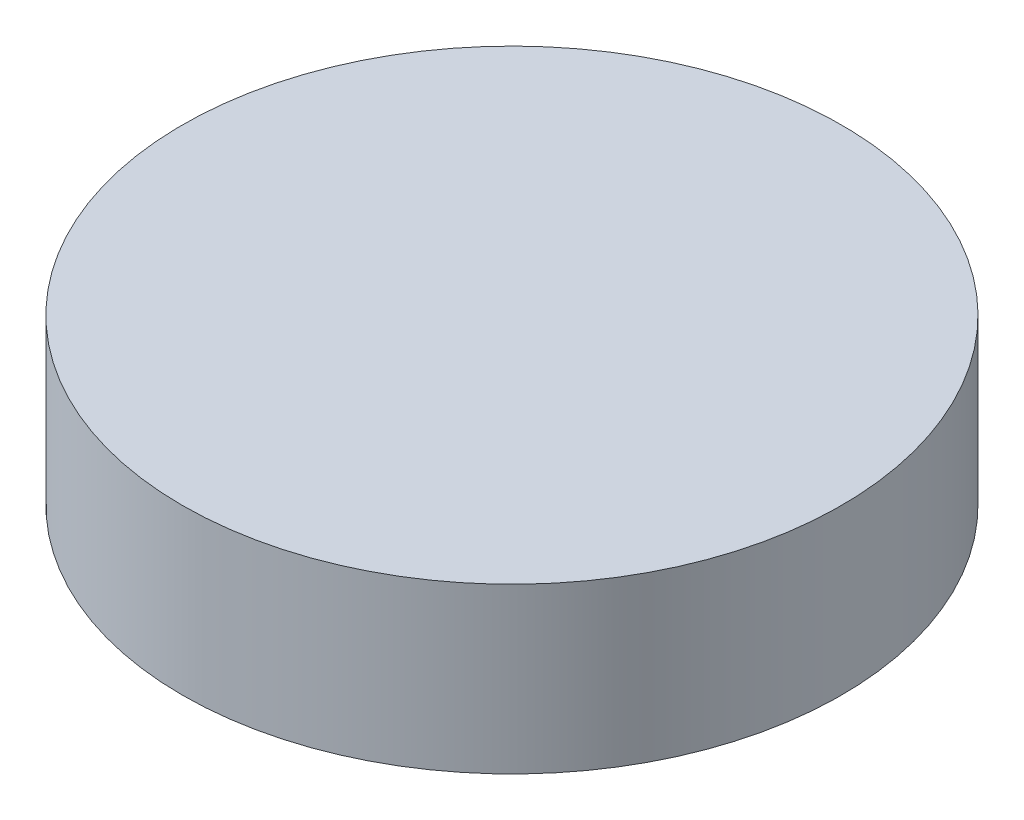
SolidWorks part; units mm, degrees
ref_plane "Front Plane" through (0, 0, 0) normal (0, 0, 1) x (1, 0, 0)
ref_plane "Top Plane" through (0, 0, 0) normal (0, 1, 0) x (1, 0, 0)
ref_plane "Right Plane" through (0, 0, 0) normal (1, 0, 0) x (0, 0, -1)
sketch "Sketch1" plane through (0, 0, 0) normal (0, 1, 0) x (1, 0, 0)
  circle A0 centre (-28.44, -17.5079) radius 12.7359
  dimension "D1" = 25.4718
extrude "Boss-Extrude1" add sketch "Sketch1" along normal blind 6.35
sketch "Sketch2" plane through (0, 6.35, 0) normal (0, 1, 0) x (1, 0, 0)
  circle A2 centre (-28.44, -17.5079) radius 12.9359
  circle A3 centre (-28.44, -17.5079) radius 12.9359
  dimension "D1" = 0.2
